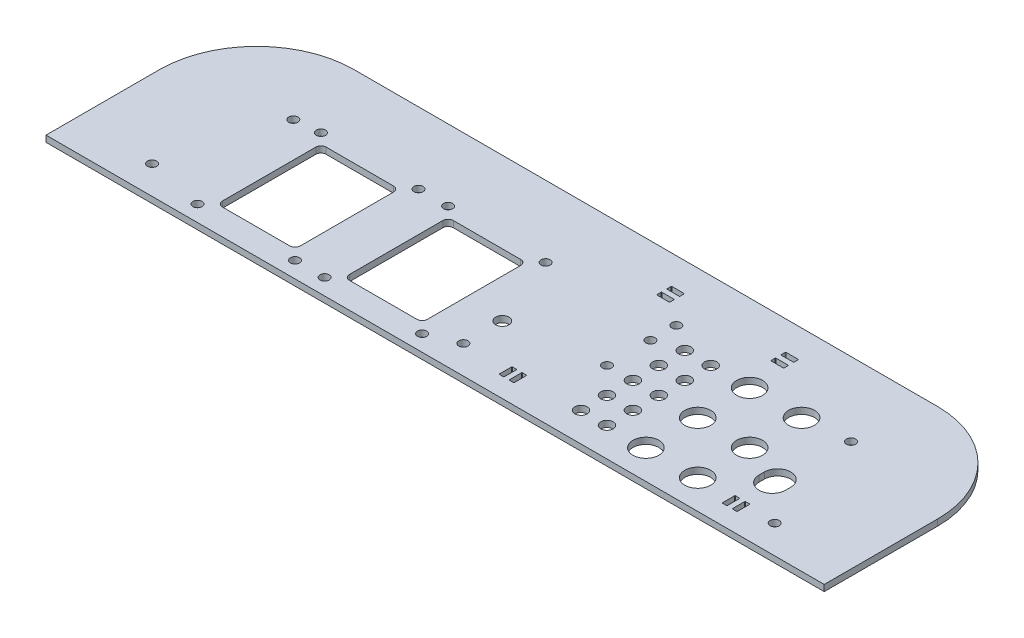
SolidWorks part; units mm, degrees
material "Acrylic (Medium-high impact)"
ref_plane "Front Plane" through (0, 0, 0) normal (0, 0, 1) x (1, 0, 0)
ref_plane "Top Plane" through (0, 0, 0) normal (0, 1, 0) x (1, 0, 0)
ref_plane "Right Plane" through (0, 0, 0) normal (1, 0, 0) x (0, 0, -1)
sketch "Sketch1" plane through (0, 0, 0) normal (0, 1, 0) x (1, 0, 0)
  line L1 (0, 0) -> (381, 0)
  line L2 (0, 0) -> (0, 55.5625)
  line L3 (47.625, 103.1875) -> (333.375, 103.1875)
  line L4 (381, 0) -> (381, 55.5625)
  arc A0 (333.375, 103.1875) -> (381, 55.5625) centre (333.375, 55.5625) cw
  arc A1 (0, 55.5625) -> (47.625, 103.1875) centre (47.625, 55.5625) cw
  dimension "D3" = 47.625
  dimension "D1" = 381
  dimension "D2" = 103.1875
extrude "Boss-Extrude1" add sketch "Sketch1" along normal blind 3.0734
sketch "Tub inner border" plane through (0, 3.0734, 0) normal (0, 1, 0) x (1, 0, 0)
  line L12 (355.6, 0) -> (355.6, 55.5625)
  line L13 (333.375, 77.7875) -> (47.625, 77.7875)
  line L14 (25.4, 55.5625) -> (25.4, 0)
  line L15 (355.6, 0) -> (355.6, 55.5625) construction
  line L16 (333.375, 77.7875) -> (47.625, 77.7875) construction
  line L17 (25.4, 55.5625) -> (25.4, 0) construction
  arc A8 (355.6, 55.5625) -> (333.375, 77.7875) centre (333.375, 55.5625) ccw
  arc A9 (47.625, 77.7875) -> (25.4, 55.5625) centre (47.625, 55.5625) ccw
  arc A10 (355.6, 55.5625) -> (333.375, 77.7875) centre (333.375, 55.5625) ccw construction
  arc A11 (47.625, 77.7875) -> (25.4, 55.5625) centre (47.625, 55.5625) ccw construction
  dimension "D1" = 25.4
hole_wizard "L Bracket Mount Holes (#8)" positions "Sketch2" profile "Sketch3" hole size "#8" standard "ANSI Inch" end condition through all
sketch "Sketch2" plane through (0, 3.0734, 0) normal (0, 1, 0) x (1, 0, 0)
  line L0 (190.5, 103.1875) -> (190.5, 0) construction
  line L1 (333.375, 103.1875) -> (47.625, 103.1875) construction
  line L2 (0, 0) -> (381, 0) construction
  line L5 (333.375, 77.7875) -> (47.625, 77.7875) construction
  point P0 (38.1, 13.8557)
  point P16 (342.9, 13.8557)
  point P17 (53.975, 67.1068)
  point P23 (327.025, 67.1068)
  point P24 (190.5, 13.8557)
  dimension "D1" = 13.8557
  dimension "D2" = 152.4
  dimension "D3" = 10.6807
  dimension "D4" = 6.35
sketch "Sketch3" plane through (38.1, 3.0734, -13.8557) normal (1, 0, 0) x (0, 0, 1)
  line L0 (0, 0) -> (0, 3.0734)
  line L1 (0, 3.0734) -> (2.2479, 3.0734)
  line L2 (2.2479, 3.0734) -> (2.2479, 0)
  line L5 (2.2479, 0) -> (0, 0)
  line L11 (0, -6.35) -> (0, 107.95) construction
  dimension "Thru Hole Dia." = 4.4958
  dimension "Thru Hole Depth" = 3.0734
sketch "Sketch4" plane through (0, 3.0734, 0) normal (0, 1, 0) x (1, 0, 0)
  line L0 (333.375, 77.7875) -> (47.625, 77.7875) construction
  line L1 (25.4, 55.5625) -> (25.4, 0) construction
  circle A0 centre (50.8, 52.3875) radius 6.35
  dimension "D1" = 12.7
  dimension "D2" = 25.4
  dimension "D3" = 25.4
extrude "Humidifier Hole" [suppressed] cut sketch "Sketch4" against normal through all
sketch "Sketch6" plane through (0, 3.0734, 0) normal (0, 1, 0) x (1, 0, 0)
  line L0 (355.6, 0) -> (355.6, 55.5625) construction
  line L1 (333.375, 77.7875) -> (47.625, 77.7875) construction
  circle A0 centre (304.8, 65.0875) radius 6.35
  dimension "D1" = 12.7
  dimension "D2" = 50.8
  dimension "D3" = 12.7
extrude "Atlas Sensors" cut sketch "Sketch6" against normal through all
pattern_linear "Atlas Sensor Pattern" count 3 spacing 25.4 along (0, 0, 1) count 2 spacing 25.4 along (-1, 0, 0) of "Atlas Sensors"
sketch "Sketch7" plane through (0, 3.0734, 0) normal (0, 1, 0) x (1, 0, 0)
  line L2 (333.375, 77.7875) -> (47.625, 77.7875) construction
  line L3 (355.6, 0) -> (355.6, 55.5625) construction
  circle A0 centre (260.35, 65.0875) radius 3.0226
  dimension "D1" = 6.0452
  dimension "D2" = 12.7
  dimension "D3" = 95.25
extrude "Nutrient Hoses" cut sketch "Sketch7" against normal through all and the other way through all
pattern_linear "LPattern2" count 2 spacing 12.7 along (-1, 0, 0) count 5 spacing 12.7 along (0, 0, 1) of "Nutrient Hoses"
hole_wizard "Water Level Sensor" positions "Sketch8" profile "Sketch9" hole size "#8" standard "ANSI Inch" end condition through all
sketch "Sketch8" plane through (0, 3.0734, 0) normal (0, 1, 0) x (1, 0, 0)
  line L1 (247.65, 39.6875) -> (234.95, 39.6875) construction
  circle A1 centre (247.65, 14.2875) radius 3.0226 construction
  point P0 (234.95, 60.9473)
  point P2 (234.95, 39.6875)
  point P17 (234.95, 73.6473)
  dimension "D1" = 21.2598
  dimension "D2" = 12.7
  dimension "D3" = 12.7
sketch "Sketch9" plane through (234.95, 3.0734, -60.9473) normal (1, 0, 0) x (0, 0, 1)
  line L0 (0, 0) -> (0, 3.0734)
  line L1 (0, 3.0734) -> (2.2479, 3.0734)
  line L2 (2.2479, 3.0734) -> (2.2479, 0)
  line L5 (2.2479, 0) -> (0, 0)
  line L11 (0, -6.35) -> (0, 107.95) construction
  dimension "Thru Hole Dia." = 4.4958
  dimension "Thru Hole Depth" = 3.0734
sketch "Sketch10" plane through (0, 3.0734, 0) normal (0, 1, 0) x (1, 0, 0)
  line L0 (321.4688, 9.779) -> (321.4688, 15.621)
  line L1 (321.7228, 15.875) -> (323.596, 15.875)
  line L2 (323.85, 15.621) -> (323.85, 9.779)
  line L3 (323.596, 9.525) -> (321.7228, 9.525)
  line L4 (325.12, 15.875) -> (325.12, 9.525) construction
  line L5 (326.644, 9.525) -> (328.5173, 9.525)
  line L6 (326.39, 15.621) -> (326.39, 9.779)
  line L7 (328.7713, 9.779) -> (328.7713, 15.621)
  line L8 (328.5173, 15.875) -> (326.644, 15.875)
  line L9 (355.6, 0) -> (355.6, 55.5625) construction
  line L10 (321.4688, 12.7) -> (328.7713, 12.7) construction
  line L11 (0, 0) -> (381, 0) construction
  line L12 (325.12, 30.48) -> (325.12, 33.02) construction
  line L13 (318.643, 30.48) -> (318.643, 33.02)
  line L14 (331.597, 30.48) -> (331.597, 33.02)
  arc A0 (323.85, 9.779) -> (323.596, 9.525) centre (323.596, 9.779) cw
  arc A1 (321.4688, 9.779) -> (321.7228, 9.525) centre (321.7228, 9.779) ccw
  arc A2 (323.596, 15.875) -> (323.85, 15.621) centre (323.596, 15.621) cw
  arc A3 (321.4688, 15.621) -> (321.7228, 15.875) centre (321.7228, 15.621) cw
  arc A4 (326.39, 9.779) -> (326.644, 9.525) centre (326.644, 9.779) ccw
  arc A5 (328.7713, 9.779) -> (328.5173, 9.525) centre (328.5173, 9.779) cw
  arc A6 (328.7713, 15.621) -> (328.5173, 15.875) centre (328.5173, 15.621) ccw
  arc A7 (326.644, 15.875) -> (326.39, 15.621) centre (326.644, 15.621) ccw
  arc A8 (318.643, 30.48) -> (331.597, 30.48) centre (325.12, 30.48) ccw
  arc A9 (331.597, 33.02) -> (318.643, 33.02) centre (325.12, 33.02) ccw
  point P14 (323.85, 9.525)
  point P17 (321.4688, 9.525)
  point P20 (323.85, 15.875)
  point P23 (321.4688, 15.875)
  point P38 (325.12, 31.75)
  dimension "D4" = 0.254
  dimension "D7" = 6.477
  dimension "D1" = 2.3813
  dimension "D2" = 6.35
  dimension "D3" = 1.27
  dimension "D5" = 30.48
  dimension "D6" = 12.7
  dimension "D8" = 2.54
  dimension "D9" = 19.05
extrude "temp sensor mounting" cut sketch "Sketch10" against normal through all
sketch "Sketch12" plane through (0, 3.0734, 0) normal (0, 1, 0) x (1, 0, 0)
  line L5 (133.35, 12.7) -> (171.45, 12.7)
  line L6 (133.35, 12.7) -> (133.35, 63.5)
  line L7 (133.35, 63.5) -> (171.45, 63.5)
  line L8 (171.45, 12.7) -> (171.45, 63.5)
  line L11 (355.6, 0) -> (355.6, 55.5625) construction
  dimension "D1" = 38.1
  dimension "D2" = 50.8
  dimension "D7" = 184.15
extrude "Accessory Hole" cut sketch "Sketch12" against normal through all
fillet "Fillet1" radius 2.54 4 edges at (171.45, 1.5367, -12.7) (171.45, 1.5367, -63.5) (133.35, 1.5367, -63.5) (133.35, 1.5367, -12.7)
hole_wizard "#8 Clearance Hole3" positions "Sketch13" profile "Sketch14" hole size "#8" standard "ANSI Inch" end condition through all
sketch "Sketch13" plane through (0, 3.0734, 0) normal (0, 1, 0) x (1, 0, 0)
  line L2 (168.91, 63.5) -> (135.89, 63.5) construction
  line L3 (133.35, 60.96) -> (133.35, 15.24) construction
  point P0 (128.524, 68.326)
  point P12 (176.276, 68.326)
  point P13 (176.276, 7.874)
  point P14 (128.524, 7.874)
  dimension "D1" = 4.826
  dimension "D2" = 4.826
  dimension "D3" = 2
  dimension "D4" = 2
sketch "Sketch14" plane through (128.524, 3.0734, -68.326) normal (1, 0, 0) x (0, 0, 1)
  line L0 (0, 0) -> (0, 3.0734)
  line L1 (0, 3.0734) -> (2.2479, 3.0734)
  line L2 (2.2479, 3.0734) -> (2.2479, 0)
  line L5 (2.2479, 0) -> (0, 0)
  line L11 (0, -6.35) -> (0, 107.95) construction
  dimension "Thru Hole Dia." = 4.4958
  dimension "Thru Hole Depth" = 3.0734
pattern_linear "LPattern3" count 2 spacing 62.23 along (-1, 0, 0) of "Accessory Hole", "Fillet1", "#8 Clearance Hole3"
sketch "Sketch15" plane through (0, 3.0734, 0) normal (0, 1, 0) x (1, 0, 0)
  line L0 (127, 7.0443) -> (127, 24.7721) construction
  line L1 (0, 55.5625) -> (0, 0) construction
  dimension "D1" = 127
sketch "Sketch16" plane through (0, 3.0734, 0) normal (0, 1, 0) x (1, 0, 0)
  line L0 (215.9, 31.75) -> (215.9, 25.4) construction
  line L1 (212.5028, 15.875) -> (214.376, 15.875)
  line L2 (212.2488, 15.621) -> (212.2488, 9.779)
  line L3 (212.5028, 9.525) -> (214.376, 9.525)
  line L4 (214.63, 15.621) -> (214.63, 9.779)
  line L6 (355.6, 0) -> (355.6, 55.5625) construction
  line L7 (219.2973, 9.525) -> (217.424, 9.525)
  line L8 (219.5513, 15.621) -> (219.5513, 9.779)
  line L9 (217.17, 15.621) -> (217.17, 9.779)
  line L10 (219.2973, 15.875) -> (217.424, 15.875)
  line L11 (321.7228, 9.525) -> (323.596, 9.525) construction
  arc A0 (212.2488, 9.779) -> (212.5028, 9.525) centre (212.5028, 9.779) ccw
  arc A1 (214.376, 9.525) -> (214.63, 9.779) centre (214.376, 9.779) ccw
  arc A2 (214.376, 15.875) -> (214.63, 15.621) centre (214.376, 15.621) cw
  arc A3 (212.5028, 15.875) -> (212.2488, 15.621) centre (212.5028, 15.621) ccw
  arc A4 (217.424, 9.525) -> (217.17, 9.779) centre (217.424, 9.779) cw
  arc A5 (219.5513, 9.779) -> (219.2973, 9.525) centre (219.2973, 9.779) cw
  arc A6 (217.424, 15.875) -> (217.17, 15.621) centre (217.424, 15.621) ccw
  arc A7 (219.2973, 15.875) -> (219.5513, 15.621) centre (219.2973, 15.621) cw
  point P12 (212.2488, 9.525)
  point P17 (214.63, 15.875)
  point P20 (212.2488, 15.875)
  dimension "D6" = 0.254
  dimension "D1" = 2.3813
  dimension "D2" = 6.35
  dimension "D3" = 1.27
  dimension "D5" = 139.7
extrude "Pump Wire zip tie" cut sketch "Sketch16" against normal through all
sketch "Sketch18" plane through (0, 3.0734, 0) normal (0, 1, 0) x (1, 0, 0)
  line L0 (245.8755, 85.4075) -> (252.2255, 85.4075) construction
  line L1 (273.304, 89.0588) -> (279.146, 89.0588)
  line L2 (273.05, 88.8048) -> (273.05, 86.9315)
  line L3 (273.304, 86.6775) -> (279.146, 86.6775)
  line L4 (279.4, 88.8048) -> (279.4, 86.9315)
  line L5 (279.4, 82.0103) -> (279.4, 83.8835)
  line L6 (273.304, 81.7563) -> (279.146, 81.7563)
  line L7 (273.05, 82.0103) -> (273.05, 83.8835)
  line L8 (273.304, 84.1375) -> (279.146, 84.1375)
  line L9 (333.375, 77.7875) -> (47.625, 77.7875) construction
  line L10 (273.05, 65.0875) -> (273.05, 103.1875) construction
  line L12 (333.375, 103.1875) -> (47.625, 103.1875) construction
  arc A0 (273.05, 86.9315) -> (273.304, 86.6775) centre (273.304, 86.9315) ccw
  arc A1 (279.146, 86.6775) -> (279.4, 86.9315) centre (279.146, 86.9315) ccw
  arc A2 (279.146, 89.0588) -> (279.4, 88.8048) centre (279.146, 88.8048) cw
  arc A3 (273.304, 89.0588) -> (273.05, 88.8048) centre (273.304, 88.8048) ccw
  arc A4 (279.146, 84.1375) -> (279.4, 83.8835) centre (279.146, 83.8835) cw
  arc A5 (279.146, 81.7563) -> (279.4, 82.0103) centre (279.146, 82.0103) ccw
  arc A6 (273.304, 81.7563) -> (273.05, 82.0103) centre (273.304, 82.0103) cw
  arc A7 (273.05, 83.8835) -> (273.304, 84.1375) centre (273.304, 83.8835) cw
  circle A9 centre (279.4, 65.0875) radius 6.35 construction
  point P10 (279.4, 86.6775)
  point P13 (279.4, 89.0588)
  point P16 (273.05, 89.0588)
  dimension "D4" = 0.254
  dimension "D1" = 2.3813
  dimension "D2" = 6.35
  dimension "D3" = 1.27
  dimension "D5" = 7.62
extrude "Wire Zip Tie" cut sketch "Sketch18" against normal through all
pattern_linear "LPattern4" count 2 spacing 55.88 along (-1, 0, 0) of "Wire Zip Tie"
hole_wizard "1/4 Clearance Hole1" positions "Sketch19" profile "Sketch20" hole size "1/4" standard "ANSI Inch" end condition through all
sketch "Sketch19" plane through (0, 3.0734, 0) normal (0, 1, 0) x (1, 0, 0)
  line L0 (190.5, 13.8557) -> (190.5, 32.9057) construction
  point P0 (190.5, 32.9057)
  dimension "D1" = 19.05
sketch "Sketch20" plane through (190.5, 3.0734, -32.9057) normal (1, 0, 0) x (0, 0, 1)
  line L0 (0, 0) -> (0, 3.0734)
  line L1 (0, 3.0734) -> (3.2639, 3.0734)
  line L2 (3.2639, 3.0734) -> (3.2639, 0)
  line L5 (3.2639, 0) -> (0, 0)
  line L11 (0, -6.35) -> (0, 107.95) construction
  dimension "Thru Hole Dia." = 6.5278
  dimension "Thru Hole Depth" = 3.0734
equation "\"Height\"= 32in"
equation "\"Width\"= 23in"
equation "\"Depth\"= 20in"
equation "\"Plexi\"= .121in"
equation "\"EBWidth\" = 9in"
equation "\"ComponentMountDia\"=0.1770"
equation "\"MagnetThickness\"= 0.125in"
equation "\"MagnetDiameter\"= 12mm"
equation "\"DoorPlexi\" = \"Plexi\""
equation "\"ShelfThickness\" = .1250in"
equation "\"BasePlateThickness\" = 0.5in"
equation "\"BasePlateWidth\" = \"Width\"+\"EBWidth\"-2*\"Plexi\""
equation "\"BasePlateDepth\" = \"TopBarDepth\"+2*\"CornerCube\""
equation "\"Boxsize\" = .75in"
equation "\"BoxsizeHalf\" = \"Boxsize\"/2"
equation "\"Boxinner\" = .625in"
equation "\"CornerCube\" = 0.75in"
equation "\"FingerLength\" = 1.125in"
equation "\"FingerWidth\" = .625in"
equation "\"Cutwidth\"= .016in"
equation "\"Earsize\"= 1in + \"Cutwidth\" /2"
equation "\"Slotsize\" = 1in - \"CutWidth\" / 2"
equation "\"InnerWidth\" = \"Width\" - 2* \"Plexi\""
equation "\"InnerHeight\" = \"Height\" -2 * \"Plexi\""
equation "\"InnerDepth\" = \"Depth\" - 2*\"Plexi\""
equation "\"FrontDoorGap\" = .1in"
equation "\"TopDepth\" = \"Depth\"-\"DoorPlexi\"-\"FrontDoorGap\""
equation "\"TopBarDepth\" = \"Depth\"-\"DoorPlexi\"-\"Plexi\"-2*\"MagnetThickness\"-2*\"CornerCube\""
equation "\"RearNumHoles\" = 4"
equation "\"RearHolesBorder\" = 2.25"
equation "\"RearHoleSpacing\" = (\"Width\" - 2*\"RearHolesBorder\") / (\"RearNumHoles\"-1)"
equation "\"RearBarLength\" = (\"InnerWidth\"-2*\"CornerCube\")"
equation "\"RearTopNumHoles\" = 4"
equation "\"RearTopHolesBorder\" = 3.1"
equation "\"RearTopHolesSpacing\" = (\"Width\" - 2*\"RearTopHolesBorder\") / (\"RearTopNumHoles\"-1)"
equation "\"SideTopNumHoles\" = 4"
equation "\"SideTopHoleOffset\"=\"CornerCube\"+\"FingerLength\"+\"Plexi\"+.5"
equation "\"SideTopHoleSpacing\" = (\"TopBarDepth\"-2*\"SideTopHoleOffset\") / (\"SideTopNumHoles\"-1)"
equation "\"SideHorizNumHoles\" = 4"
equation "\"SideHorizHoleBorder\" = 1.50"
equation "\"SideHorizHoleSpacing\" = (\"TopBarDepth\"-2*\"SideHorizHoleBorder\") / (\"SideHorizNumHoles\"-1)"
equation "\"SideVertBarLength\"=\"Height\"-\"BasePlateThickness\"-2*\"CornerCube\"-\"Plexi\""
equation "\"SideVertNumHoles\" = 4"
equation "\"SideVertHolesBorder\" = \"CornerCube\"+\"FingerLength\"+1.50"
equation "\"SideVertHoleSpacing\" = (\"SideVertBarLength\" - 2*(\"SideVertHolesBorder\"-\"Plexi\"-\"CornerCube\")) / (\"SideVertNumHoles\"-1)"
equation "\"RearSideVertNumHoles\" = 4"
equation "\"RearSideVertHolesBorder\" = 2.4"
equation "\"RearSideVertHoleSpacing\" = (\"SideVertBarLength\" - 2*(\"RearSideVertHolesBorder\"-\"Plexi\"-\"CornerCube\")) / (\"RearSideVertNumHoles\"-1)"
equation "\"Rivet3_16Dia\" = .191in"
equation "\"RivetDia\" = .228in"
equation "\"BinderPostDia\" = .228in"
equation "\"SlotDepth\" = \"Plexi\" + 0.75in + .005in"
equation "\"SideSlotWidth\"   = \"Plexi\"+.005in"
equation "\"SidePanelVertSpacing\" = (\"Height\"-2*(1.75-\"Plexi\")) / 5"
equation "\"BottomPanelSideHoleSpacing\" = (\"InnerDepth\"-2*(1.75-\"Plexi\")) / 4"
equation "\"CoolerDepth\" = 12in"
equation "\"ShelfGap\" = 0.5in"
equation "\"ShelfDepth\" = \"TopBarDepth\"+\"CornerCube\"-\"CoolerDepth\""
equation "\"ShelfBarDepth\"=\"ShelfDepth\"-2*\"CornerCube\""
equation "\"ShelfWidth\" = \"EBWidth\"-\"ShelfGap\""
equation "\"ShelfBarWidth\" = \"EBWidth\"-\"Boxsize\""
equation "\"ShelfBarWidthShort\" = \"ShelfBarWidth\"-\"Boxsize\"-\"ShelfGap\""
equation "\"ShelfHeight1\" = 13in"
equation "\"ShelfHeight2\" = 24in"
equation "\"IntakeWidth\"=4in"
equation "\"IntakeHeight\"=2in"
equation "\"ExhaustWidth\"=4in"
equation "\"ExhaustHeight\"=2in"
equation "\"VentSpacing\"=7in"
equation "\"VentVertLocation\"=12.75in"
equation "\"AngleBracketLengthShort\"=.625in"
equation "\"AngleBracketLengthLong\"=1in"
equation "\"AngleBracketWidth\"=.5in"
equation "\"AngleBracketThickness\"=.125in"
equation "\"AngleBracketHolePosShort\"=.358in"
equation "\"AngleBracketHolePosLong\"=.7in"
equation "\"AngleBracketHoleDia\"=\"Rivet3_16Dia\""
equation "\"ShelfBarAngleHole\"=\"ShelfGap\"+\"Boxsize\"+\"AngleBracketHolePosShort\""
equation "\"PSBracketThickness\" = .0641in"
equation "\"EBForwardMountOffset\" = 4.0in"
equation "\"EBForwardMount\" = 2*\"Boxsize\"+\"CoolerDepth\"+\"EBForwardMountOffset\""
equation "\"EBRearwardMountOffset\" = 1.5in"
equation "\"EBRearwardMount\"= \"Boxsize\"+\"EBRearwardMountOffset\""
equation "\"MagSealWidth\" = \"InnerWidth\""
equation "\"MagSealHeight\" = \"Height\"-\"BasePlateThickness\"-\"Plexi\""
equation "\"MagWidth\" = .500in"
equation "\"SiliconeSealOD\" = .3125in"
equation "\"SiliconeSealID\" = .1875in"
equation "\"SiliconeSealWidth\" = \"MagSealWidth\" - 2*\"MagWidth\"-\"SiliconeSealOD\""
equation "\"SiliconeSealHeigth\" = \"MagSealHeight\" - 2*\"MagWidth\"-\"SiliconeSealOD\""
equation "\"HooknLoopThick\" = .085in"
equation "\"HooknLoopWidth\" = 0.75in"
equation "\"HooknLoopHeigth\" = 0.75in"
equation "\"RivNutHeight\" = 0.015in"
equation "\"D1@Boss-Extrude1\"=\"Plexi\""
